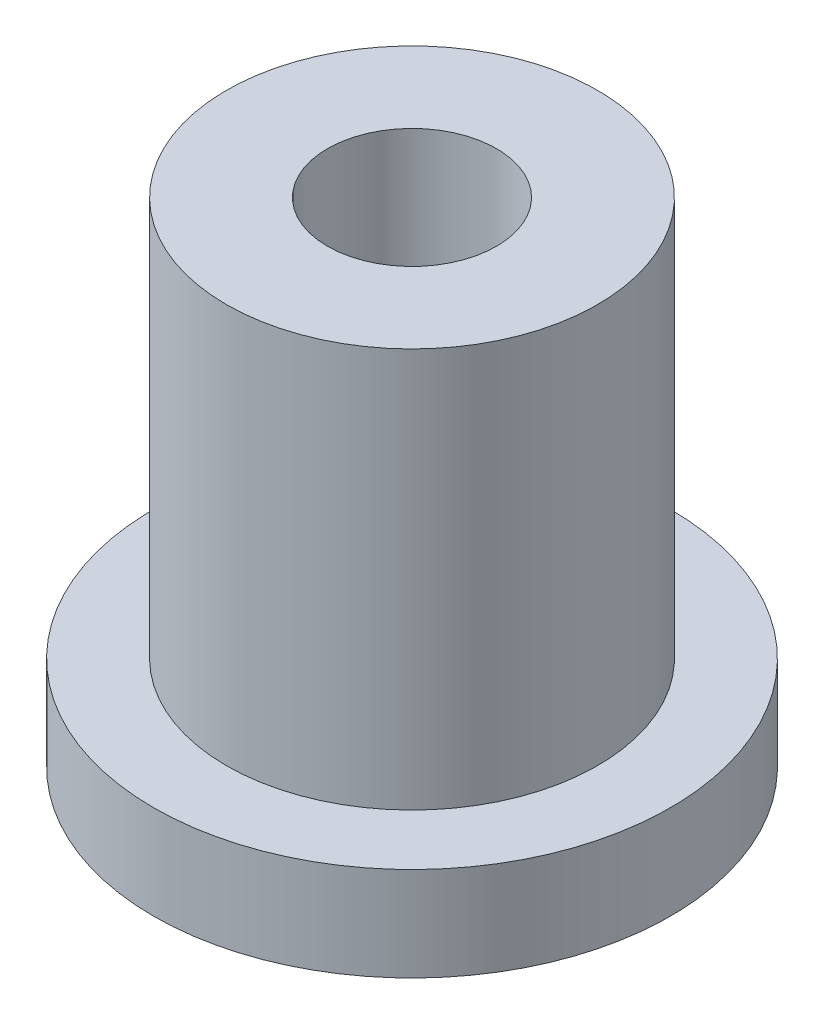
SolidWorks part; units mm, degrees
ref_plane "Front Plane" through (0, 0, 0) normal (0, 0, 1) x (1, 0, 0)
ref_plane "Top Plane" through (0, 0, 0) normal (0, 1, 0) x (1, 0, 0)
ref_plane "Right Plane" through (0, 0, 0) normal (1, 0, 0) x (0, 0, -1)
sketch "Sketch1" plane through (0, 0, 0) normal (0, 1, 0) x (1, 0, 0)
  circle A0 centre (0, 0) radius 5.5
  circle A1 centre (0, 0) radius 1.8
  dimension "D1" = 11
  dimension "D2" = 3.6
extrude "Boss-Extrude1" add sketch "Sketch1" along normal blind 2
sketch "Sketch2" plane through (0, 2, 0) normal (0, 1, 0) x (1, 0, 0)
  circle A0 centre (0, 0) radius 3.95
  circle A1 centre (0, 0) radius 1.8 construction
  circle A2 centre (0, 0) radius 1.8
  dimension "D1" = 7.9
extrude "Boss-Extrude2" add sketch "Sketch2" along normal blind 8.5
equation "\"D1@Boss-Extrude2\"=11-2.50mm"
